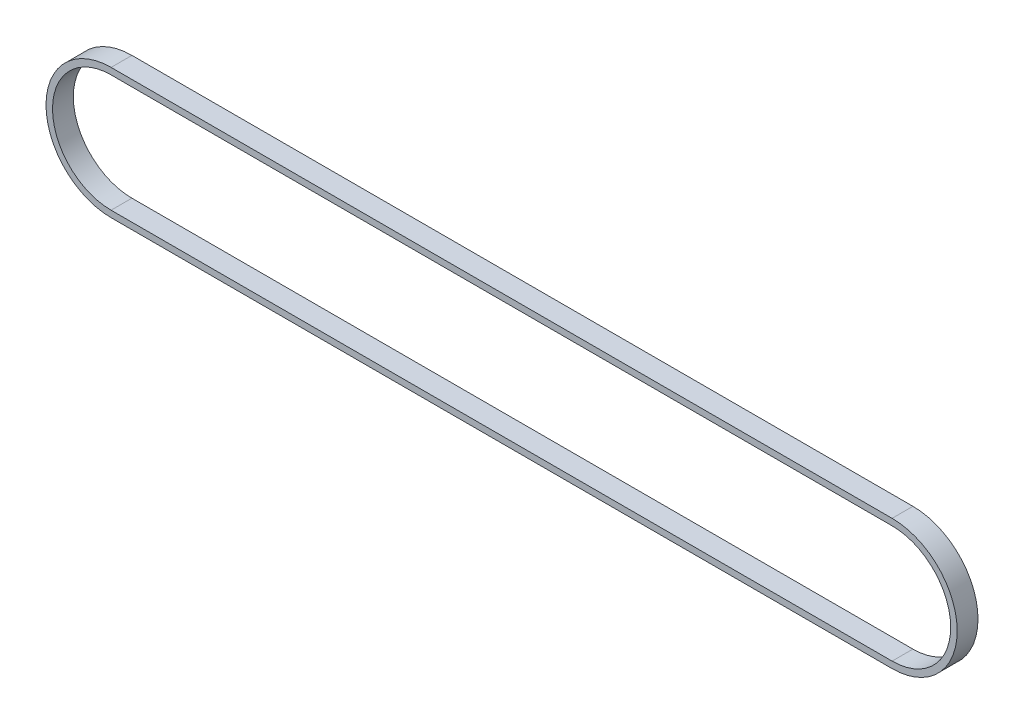
SolidWorks part; units mm, degrees
ref_plane "Front Plane" through (0, 0, 0) normal (0, 0, 1) x (1, 0, 0)
ref_plane "Top Plane" through (0, 0, 0) normal (0, 1, 0) x (1, 0, 0)
ref_plane "Right Plane" through (0, 0, 0) normal (1, 0, 0) x (0, 0, -1)
sketch "Sketch1" plane through (0, 0, 0) normal (0, 0, 1) x (1, 0, 0)
  line L0 (-75, 0) -> (75, 0) construction
  line L1 (-75, 12.5) -> (75, 12.5)
  line L2 (-75, -12.5) -> (75, -12.5)
  line L3 (-75, 11.25) -> (75, 11.25)
  line L4 (-75, -11.25) -> (75, -11.25)
  arc A0 (-75, 12.5) -> (-75, -12.5) centre (-75, 0) ccw
  arc A1 (75, -12.5) -> (75, 12.5) centre (75, 0) ccw
  arc A2 (75, -11.25) -> (75, 11.25) centre (75, 0) ccw
  arc A3 (-75, 11.25) -> (-75, -11.25) centre (-75, 0) ccw
  point P2 (0, 0)
  dimension "D2" = 12.5
  dimension "D1" = 150
  dimension "D3" = 1.25
extrude "Boss-Extrude1" add sketch "Sketch1" along normal mid plane 4
